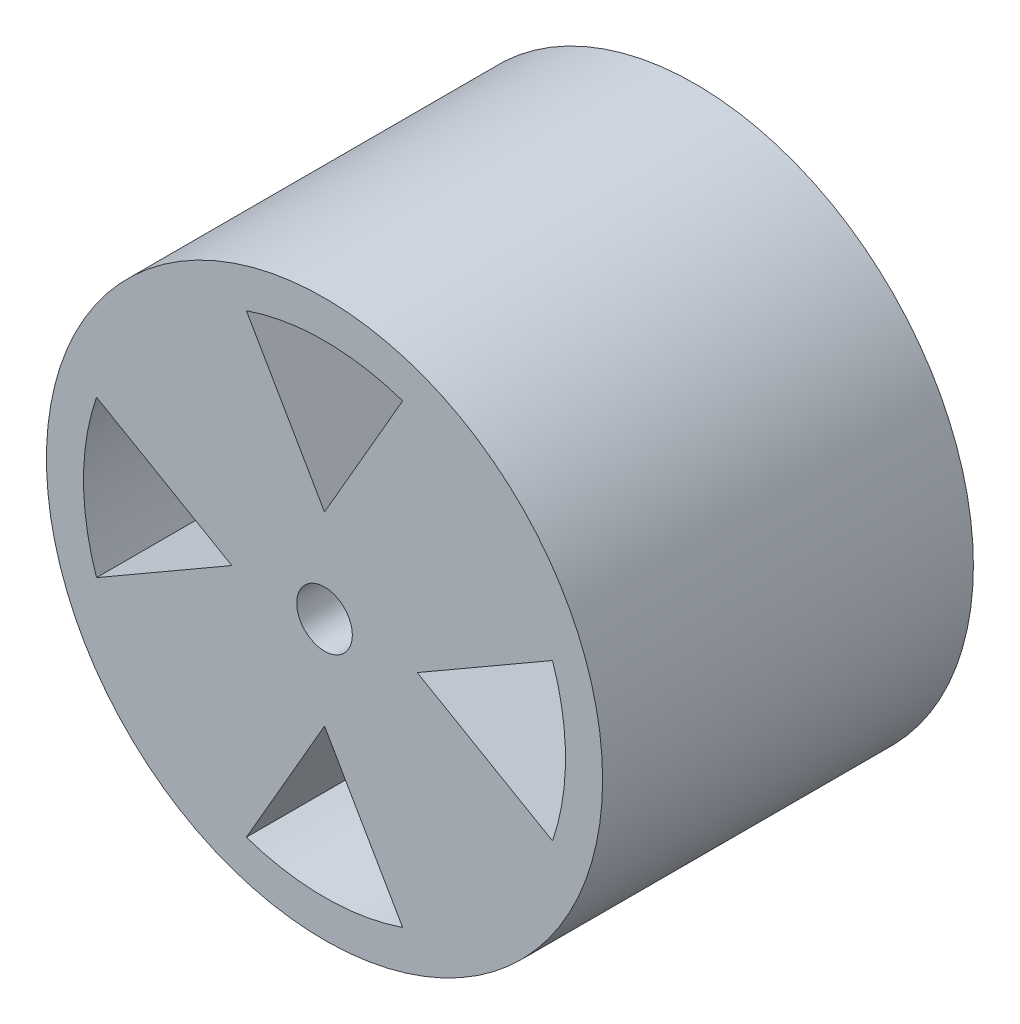
SolidWorks part; units mm, degrees
ref_plane "Front Plane" through (0, 0, 0) normal (0, 0, 1) x (1, 0, 0)
ref_plane "Top Plane" through (0, 0, 0) normal (0, 1, 0) x (1, 0, 0)
ref_plane "Right Plane" through (0, 0, 0) normal (1, 0, 0) x (0, 0, -1)
sketch "Sketch1" plane through (0, 0, 0) normal (0, 0, 1) x (1, 0, 0)
  line L0 (0, 11.2117) -> (0, -10.6658) construction
  circle A0 centre (0, 0) radius 7.5
  circle A1 centre (0, 0) radius 0.75
  dimension "17,5" = 15
  dimension "D2" = 1.5
extrude "Boss-Extrude1" add sketch "Sketch1" along normal blind 10
sketch "Sketch2" plane through (0, 0, 10) normal (0, 0, 1) x (1, 0, 0)
  line L0 (0, -2.5) -> (-2.1068, -6.1491)
  line L1 (0, -2.5) -> (2.1068, -6.1491)
  line L2 (0, -2.5) -> (0, -6.5) construction
  line L3 (-2.5, 0) -> (-6.1491, -2.1068)
  line L4 (-2.5, 0) -> (-6.1491, 2.1068)
  line L5 (0, 2.5) -> (-2.1068, 6.1491)
  line L6 (0, 2.5) -> (2.1068, 6.1491)
  line L7 (2.5, 0) -> (6.1491, 2.1068)
  line L8 (2.5, 0) -> (6.1491, -2.1068)
  circle A0 centre (0, 0) radius 6.5
  circle A1 centre (0, 0) radius 2.5
  point P20 (0, 0)
  dimension "D1" = 13
  dimension "D2" = 5
  dimension "D3" = 60
  dimension "D4" = 30
  dimension "D5" = 4
extrude "Cut-Extrude1" cut sketch "Sketch2" against normal through all contours L4 A0 L3 | L2 L0 A0 | L8 A0 L7 | L1 L2 A0 | L6 A0 L5
